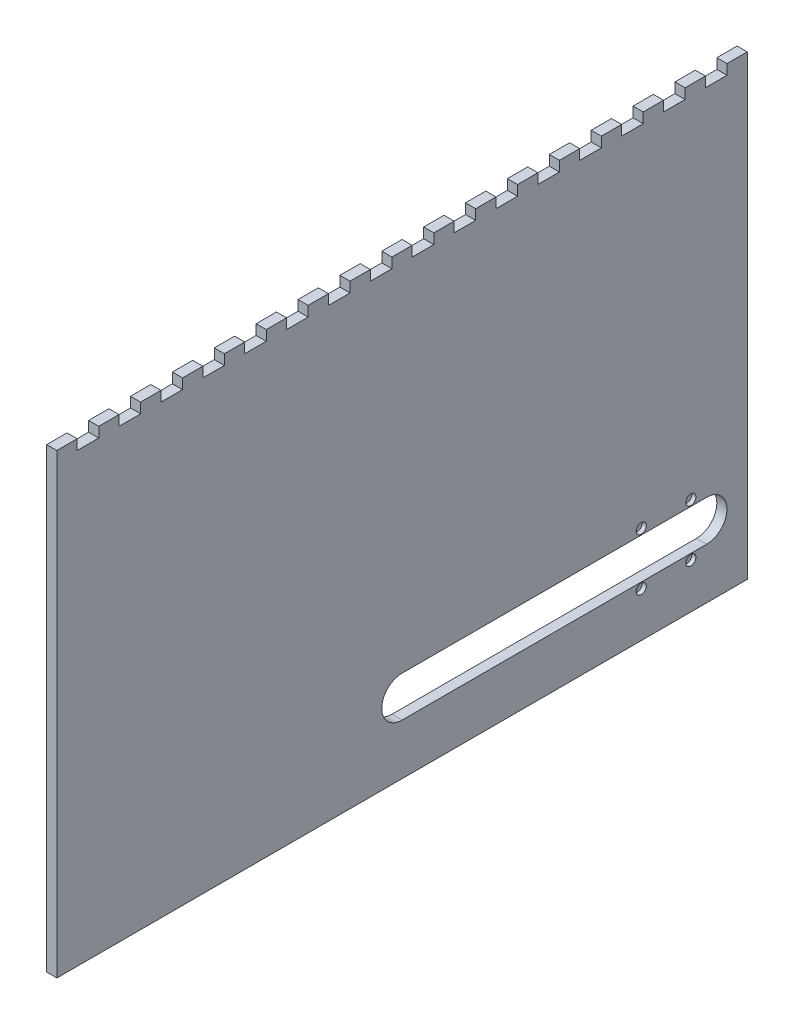
SolidWorks part; units mm, degrees
material "Acrylic (Medium-high impact)"
ref_plane "Front" through (0, 0, 0) normal (0, 0, 1) x (1, 0, 0)
ref_plane "Top" through (0, 0, 0) normal (0, 1, 0) x (1, 0, 0)
ref_plane "Right" through (0, 0, 0) normal (1, 0, 0) x (0, 0, -1)
sketch "Sketch1" plane through (0, 0, 0) normal (1, 0, 0) x (0, 0, -1)
  line L1 (-215.9, 142.875) -> (215.9, 142.875)
  line L2 (-215.9, 142.875) -> (-215.9, -142.875)
  line L3 (-215.9, -142.875) -> (215.9, -142.875)
  line L4 (215.9, 142.875) -> (215.9, -142.875)
  point P4 (-215.9, 0)
  point P6 (0, 142.875)
  dimension "D1" = 285.75
  dimension "D2" = 431.8
extrude "Boss-Extrude1" add sketch "Sketch1" along normal blind 6.35
sketch "Sketch2" plane through (6.35, 0, 0) normal (1, 0, 0) x (0, 0, -1)
  line L0 (215.9, -142.875) -> (215.9, 142.875) construction
  line L1 (-215.9, 142.875) -> (215.9, 142.875)
  line L2 (-215.9, 142.875) -> (-215.9, 136.525)
  line L3 (-215.9, 136.525) -> (215.9, 136.525)
  line L4 (215.9, 142.875) -> (215.9, 136.525)
  dimension "D1" = 6.35
extrude "Boss-Extrude2" add sketch "Sketch2" along normal blind 12.7
sketch "Sketch3" plane through (0, 0, 0) normal (-1, 0, 0) x (0, 0, 1)
  line L0 (-190.5, -85.725) -> (0, -85.725)
  line L1 (0, -111.125) -> (-190.5, -111.125)
  line L2 (38.1, 142.875) -> (38.1, -142.875) construction
  line L3 (-215.9, 142.875) -> (215.9, 142.875) construction
  line L4 (215.9, -142.875) -> (-215.9, -142.875) construction
  line L5 (215.9, 142.875) -> (215.9, -142.875) construction
  arc A0 (0, -85.725) -> (0, -111.125) centre (0, -98.425) cw
  arc A1 (-190.5, -111.125) -> (-190.5, -85.725) centre (-190.5, -98.425) cw
  dimension "D1" = 25.4
  dimension "D3" = 190.5
  dimension "D2" = 38.1
  dimension "D4" = 177.8
  dimension "D5" = 44.45
extrude "Cut-Extrude1" cut sketch "Sketch3" against normal through all
sketch "Sketch4" plane through (0, 0, 0) normal (-1, 0, 0) x (0, 0, 1)
  line L0 (-189.7062, 142.875) -> (-177.0062, 142.875)
  line L1 (-215.9, 142.875) -> (-203.2, 142.875)
  line L2 (-215.9, 142.875) -> (-215.9, 136.525)
  line L3 (-215.9, 136.525) -> (-203.2, 136.525)
  line L4 (-203.2, 142.875) -> (-203.2, 136.525)
  line L5 (-189.7062, 142.875) -> (-189.7062, 136.525)
  line L6 (-189.7062, 136.525) -> (-177.0062, 136.525)
  line L7 (-177.0062, 142.875) -> (-177.0062, 136.525)
  line L8 (-163.5125, 142.875) -> (-150.8125, 142.875)
  line L9 (-163.5125, 142.875) -> (-163.5125, 136.525)
  line L10 (-163.5125, 136.525) -> (-150.8125, 136.525)
  line L11 (-150.8125, 142.875) -> (-150.8125, 136.525)
  line L12 (-137.3187, 142.875) -> (-124.6187, 142.875)
  line L13 (-137.3187, 142.875) -> (-137.3187, 136.525)
  line L14 (-137.3187, 136.525) -> (-124.6187, 136.525)
  line L15 (-124.6187, 142.875) -> (-124.6187, 136.525)
  line L16 (-111.125, 142.875) -> (-98.425, 142.875)
  line L17 (-111.125, 142.875) -> (-111.125, 136.525)
  line L18 (-111.125, 136.525) -> (-98.425, 136.525)
  line L19 (-98.425, 142.875) -> (-98.425, 136.525)
  line L20 (-84.9312, 142.875) -> (-72.2312, 142.875)
  line L21 (-84.9312, 142.875) -> (-84.9312, 136.525)
  line L22 (-84.9312, 136.525) -> (-72.2312, 136.525)
  line L23 (-72.2312, 142.875) -> (-72.2312, 136.525)
  line L24 (-58.7375, 142.875) -> (-46.0375, 142.875)
  line L25 (-58.7375, 142.875) -> (-58.7375, 136.525)
  line L26 (-58.7375, 136.525) -> (-46.0375, 136.525)
  line L27 (-46.0375, 142.875) -> (-46.0375, 136.525)
  line L28 (-32.5437, 142.875) -> (-19.8437, 142.875)
  line L29 (-32.5437, 142.875) -> (-32.5437, 136.525)
  line L30 (-32.5437, 136.525) -> (-19.8437, 136.525)
  line L31 (-19.8437, 142.875) -> (-19.8437, 136.525)
  line L32 (-6.35, 142.875) -> (6.35, 142.875)
  line L33 (-6.35, 142.875) -> (-6.35, 136.525)
  line L34 (-6.35, 136.525) -> (6.35, 136.525)
  line L35 (6.35, 142.875) -> (6.35, 136.525)
  line L36 (19.8438, 142.875) -> (32.5438, 142.875)
  line L37 (19.8438, 142.875) -> (19.8438, 136.525)
  line L38 (19.8438, 136.525) -> (32.5438, 136.525)
  line L39 (32.5438, 142.875) -> (32.5438, 136.525)
  line L40 (46.0375, 142.875) -> (58.7375, 142.875)
  line L41 (46.0375, 142.875) -> (46.0375, 136.525)
  line L42 (46.0375, 136.525) -> (58.7375, 136.525)
  line L43 (58.7375, 142.875) -> (58.7375, 136.525)
  line L44 (72.2313, 142.875) -> (84.9313, 142.875)
  line L45 (72.2313, 142.875) -> (72.2313, 136.525)
  line L46 (72.2313, 136.525) -> (84.9313, 136.525)
  line L47 (84.9313, 142.875) -> (84.9313, 136.525)
  line L48 (98.425, 142.875) -> (111.125, 142.875)
  line L49 (98.425, 142.875) -> (98.425, 136.525)
  line L50 (98.425, 136.525) -> (111.125, 136.525)
  line L51 (111.125, 142.875) -> (111.125, 136.525)
  line L52 (124.6188, 142.875) -> (137.3187, 142.875)
  line L53 (124.6188, 142.875) -> (124.6188, 136.525)
  line L54 (124.6188, 136.525) -> (137.3187, 136.525)
  line L55 (137.3187, 142.875) -> (137.3187, 136.525)
  line L56 (150.8125, 142.875) -> (163.5125, 142.875)
  line L57 (150.8125, 142.875) -> (150.8125, 136.525)
  line L58 (150.8125, 136.525) -> (163.5125, 136.525)
  line L59 (163.5125, 142.875) -> (163.5125, 136.525)
  line L60 (177.0062, 142.875) -> (189.7062, 142.875)
  line L61 (177.0062, 142.875) -> (177.0062, 136.525)
  line L62 (177.0062, 136.525) -> (189.7062, 136.525)
  line L63 (189.7062, 142.875) -> (189.7062, 136.525)
  line L64 (203.2, 142.875) -> (215.9, 142.875)
  line L65 (203.2, 142.875) -> (203.2, 136.525)
  line L66 (203.2, 136.525) -> (215.9, 136.525)
  line L67 (215.9, 142.875) -> (215.9, 136.525)
  line L69 (-215.9, 142.875) -> (215.9, 142.875)
  line L70 (-215.9, 142.875) -> (-215.9, 136.525)
  line L71 (-215.9, 136.525) -> (215.9, 136.525)
  line L72 (215.9, 142.875) -> (215.9, 136.525)
  line M74 (215.9, 142.875) -> (-215.9, 142.875)
  dimension "D1" = 6.35
  dimension "D2" = 12.7
  dimension "D3" = 17
sketch "Sketch5" plane through (0, 0, -215.9) normal (0, 0, -1) x (-1, 0, 0)
  line L1 (-6.35, 136.525) -> (-57.7651, 136.525)
  line L2 (-6.35, 136.525) -> (-6.35, 157.6842)
  line L3 (-6.35, 157.6842) -> (-57.7651, 157.6842)
  line L4 (-57.7651, 136.525) -> (-57.7651, 157.6842)
extrude "Cut-Extrude2" cut sketch "Sketch5" against normal through all
extrude "Cut-Extrude3" cut sketch "Sketch4" against normal blind 6.35 contours L4 L71 L5 M74 | L7 L71 L9 M74 | L11 L71 L13 M74 | L15 L71 L17 M74 | L19 L71 L21 M74 | L23 L71 L25 M74 | L27 L71 L29 M74 | L31 L71 L33 M74 | L35 L71 L37 M74 | L39 L71 L41 M74 | L43 L71 L45 M74 | L47 L71 L49 M74 | L51 L71 L53 M74 | L55 L71 L57 M74 | L59 L71 L61 M74 | L63 L71 L65 M74 | L69
sketch "Sketch6" plane through (6.35, 0, 0) normal (1, 0, 0) x (0, 0, -1)
  line L0 (154.1, -100.965) -> (154.1, -95.885)
  line L1 (176.1, -95.885) -> (176.1, -100.965)
  line L2 (148.1, -116.465) -> (148.1, -111.385)
  line L3 (151.1, -116.465) -> (151.1, -111.385)
  line L4 (148.1, -85.465) -> (148.1, -80.385)
  line L5 (151.1, -85.465) -> (151.1, -80.385)
  line L6 (165.1, -95.885) -> (165.1, -100.965) construction
  line L7 (182.1, -116.465) -> (182.1, -111.385)
  line L8 (179.1, -116.465) -> (179.1, -111.385)
  line L9 (179.1, -85.465) -> (179.1, -80.385)
  line L10 (182.1, -85.465) -> (182.1, -80.385)
  line L11 (-215.9, 142.875) -> (-215.9, -142.875) construction
  line L12 (-215.9, -142.875) -> (215.9, -142.875) construction
  arc A0 (154.1, -100.965) -> (176.1, -100.965) centre (165.1, -100.965) ccw
  arc A1 (176.1, -95.885) -> (154.1, -95.885) centre (165.1, -95.885) ccw
  arc A2 (148.1, -116.465) -> (151.1, -116.465) centre (149.6, -116.465) ccw
  arc A3 (151.1, -111.385) -> (148.1, -111.385) centre (149.6, -111.385) ccw
  arc A4 (148.1, -85.465) -> (151.1, -85.465) centre (149.6, -85.465) ccw
  arc A5 (151.1, -80.385) -> (148.1, -80.385) centre (149.6, -80.385) ccw
  arc A6 (182.1, -116.465) -> (179.1, -116.465) centre (180.6, -116.465) cw
  arc A7 (179.1, -111.385) -> (182.1, -111.385) centre (180.6, -111.385) cw
  arc A8 (182.1, -85.465) -> (179.1, -85.465) centre (180.6, -85.465) cw
  arc A9 (179.1, -80.385) -> (182.1, -80.385) centre (180.6, -80.385) cw
  circle A10 centre (149.6, -82.06) radius 3.175
  circle A11 centre (180.6, -82.06) radius 3.175
  circle A12 centre (149.6, -114.79) radius 3.175
  circle A13 centre (180.6, -114.79) radius 3.175
  point P37 (165.1, -98.425)
  point P38 (176.1, -98.425)
  point P44 (0, 0)
  point P45 (0, 0)
  point P46 (0, 0)
  point P47 (0, 0)
  point P48 (180.6, -82.5419)
  point P49 (0, 0)
  point P50 (139.3084, -74.1139)
  point P51 (0, 0)
  point P52 (180.6, -74.0538)
  point P53 (180.6, -124.401)
  point P54 (149.6, -69.7719)
  point P55 (149.6, -72.5453)
  point P56 (149.6, -82.523)
  point P57 (180.6, -113.7532)
  dimension "D5" = 1.5
  dimension "D9" = 1.5
  dimension "D12" = 6.35
  dimension "D1" = 5.08
  dimension "D2" = 5.08
  dimension "D3" = 15.5
  dimension "D4" = 15.5
  dimension "D6" = 15.5
  dimension "D7" = 15.5
  dimension "D8" = 5.08
  dimension "D10" = 381
  dimension "D11" = 44.45
extrude "Cut-Extrude5" cut sketch "Sketch6" against normal blind 2.54 contours L5 A10 A5 | L4 A10 L5 A5 | A5 A10 L4 | L9 A11 L10 A9 | A9 A11 L9 | L10 A11 A9 | A2 A12 L3 | L3 A12 L2 A2 | L2 A12 A2 | L7 A13 L8 A6 | A6 A13 L7 | L8 A13 A6
